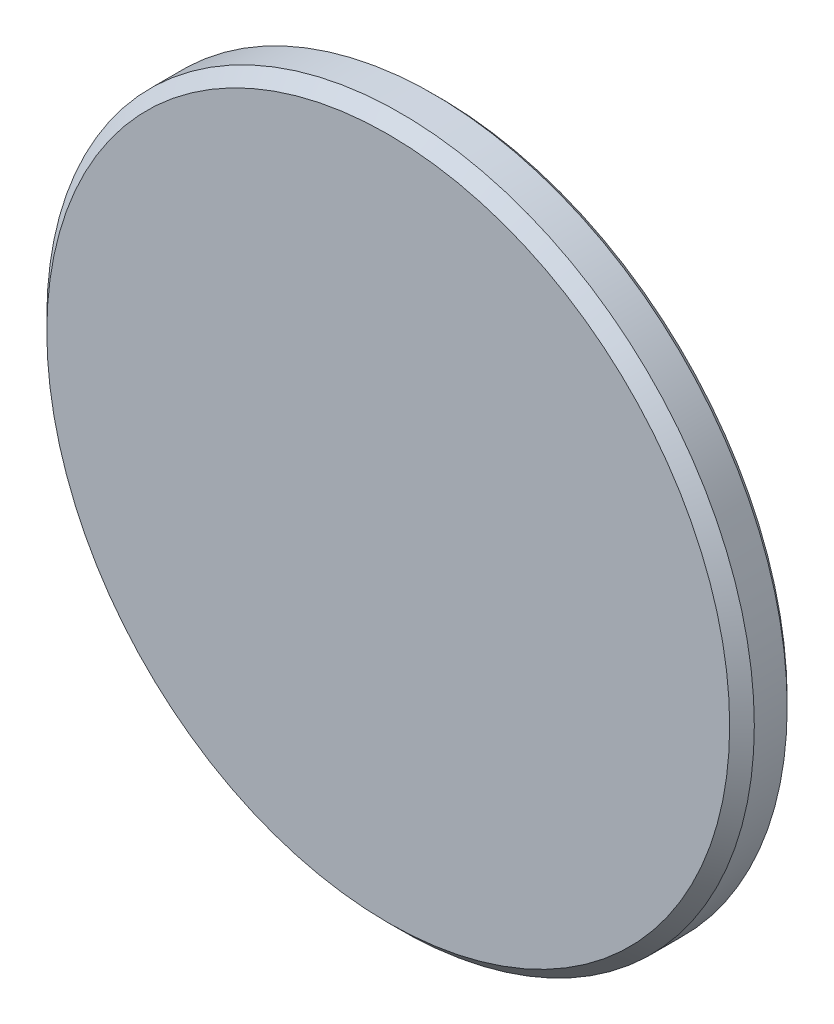
SolidWorks part; units mm, degrees
material "Glass"
ref_plane "Front Plane" through (0, 0, 0) normal (0, 0, 1) x (1, 0, 0)
ref_plane "Top Plane" through (0, 0, 0) normal (0, 1, 0) x (1, 0, 0)
ref_plane "Right Plane" through (0, 0, 0) normal (1, 0, 0) x (0, 0, -1)
sketch "Sketch1" plane through (0, 0, 0) normal (0, 1, 0) x (1, 0, 0)
  line L0 (21.4884, 0) -> (0, 0)
  line L1 (0, 0) -> (0, -3.175)
  line L2 (0, -3.175) -> (21.1074, -3.175)
  line L3 (21.1074, -3.175) -> (21.8694, -2.413)
  line L4 (21.8694, -2.413) -> (21.8694, -0.381)
  line L5 (21.8694, -0.381) -> (21.4884, 0)
  line L6 (0, 0) -> (0, -3.175) construction
revolve "Revolve1" add sketch "Sketch1" angle 360 about L6
